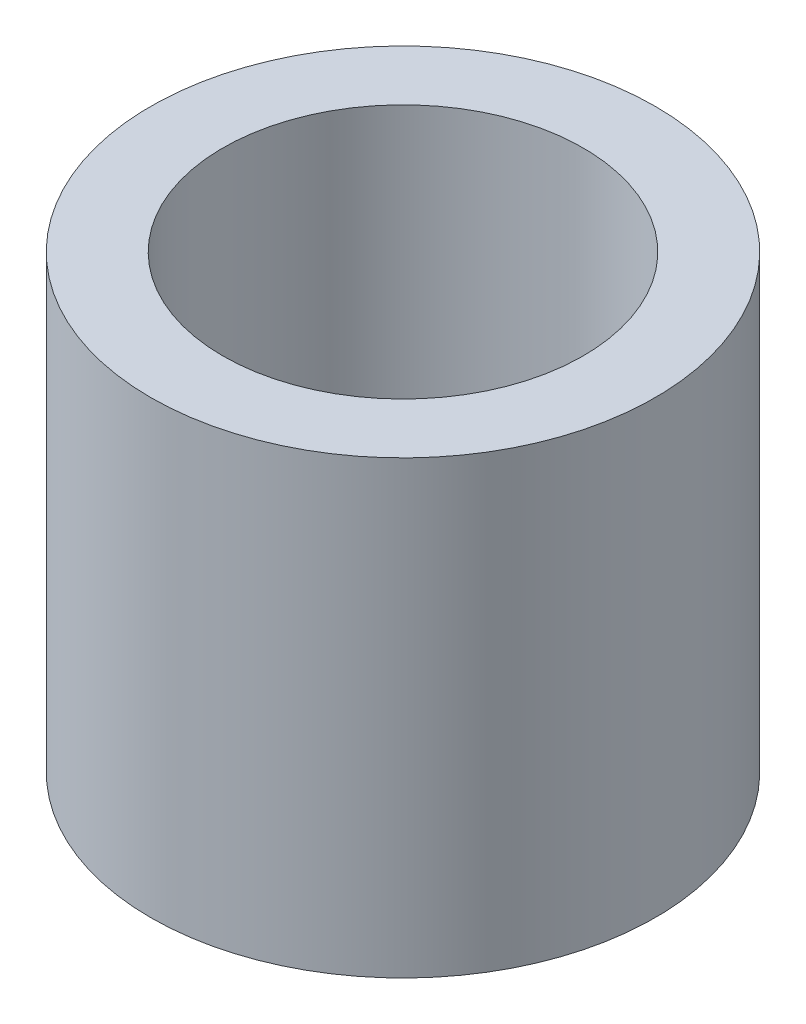
SolidWorks part; units mm, degrees
ref_plane "Front Plane" through (0, 0, 0) normal (0, 0, 1) x (1, 0, 0)
ref_plane "Top Plane" through (0, 0, 0) normal (0, 1, 0) x (1, 0, 0)
ref_plane "Right Plane" through (0, 0, 0) normal (1, 0, 0) x (0, 0, -1)
sketch "Sketch1" plane through (0, 0, 0) normal (0, 1, 0) x (1, 0, 0)
  circle A0 centre (0, 0) radius 1
  circle A2 centre (0, 0) radius 1.4
  dimension "D1" = 2
  dimension "D2" = 2.8
extrude "Boss-Extrude1" add sketch "Sketch1" along normal blind 2.5
